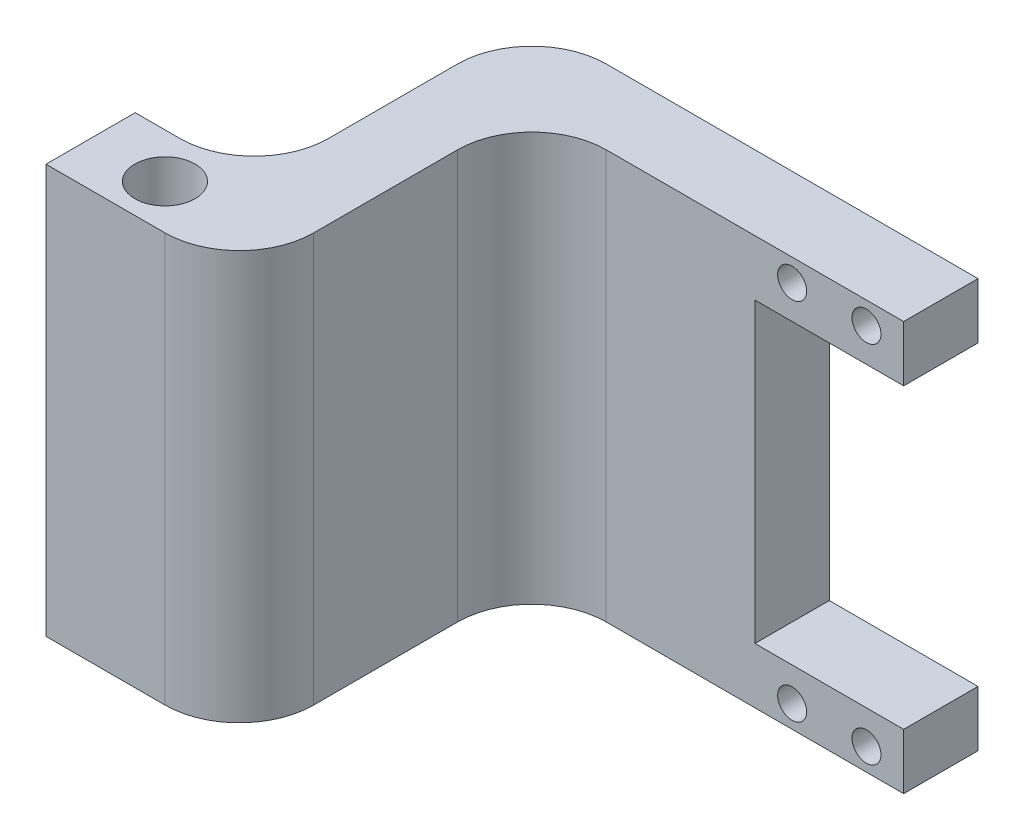
SolidWorks part; units mm, degrees
ref_plane "Ebene vorne" through (0, 0, 0) normal (0, 0, 1) x (1, 0, 0)
ref_plane "Ebene oben" through (0, 0, 0) normal (0, 1, 0) x (1, 0, 0)
ref_plane "Ebene rechts" through (0, 0, 0) normal (1, 0, 0) x (0, 0, -1)
sketch "Sketch1" plane through (0, 0, 0) normal (0, 0, 1) x (1, 0, 0)
  line L0 (-10, 24.5) -> (10, 24.5) construction
  line L5 (10, -20) -> (-10, -20)
  line L6 (10, -20) -> (10, 20) construction
  line L15 (10, 20) -> (-10, 20)
  line L16 (-10, -20) -> (-10, 20)
  line L17 (10, -20) -> (-10, 20) construction
  line L18 (10, 20) -> (-10, -20) construction
  line L19 (-10, 20) -> (10, 20)
  line L20 (-10, 20) -> (-10, 27.5)
  line L21 (-10, 27.5) -> (10, 27.5)
  line L22 (10, 20) -> (10, 27.5)
  line L23 (-10, 0) -> (10, 0) construction
  line L24 (-10, -24.5) -> (10, -24.5) construction
  line L25 (10, -20) -> (10, -27.5)
  line L26 (-10, -27.5) -> (10, -27.5)
  line L27 (-10, -20) -> (-10, -27.5)
  line L28 (-10, -20) -> (10, -20)
  line L29 (10, -20) -> (-10, -20)
  line L31 (-10, 27.5) -> (-40, 27.5)
  line L32 (-10, 27.5) -> (-10, -27.5)
  line L33 (-10, -27.5) -> (-40, -27.5)
  line L34 (-40, 27.5) -> (-40, -27.5)
  circle A0 centre (-5, 24.5) radius 1.95
  circle A1 centre (5, 24.5) radius 1.95
  circle A2 centre (5, -24.5) radius 1.95
  circle A3 centre (-5, -24.5) radius 1.95
  point P0 (0, 0)
  dimension "D5" = 3.9
  dimension "D1" = 20
  dimension "D2" = 40
  dimension "D3" = 7.5
  dimension "D4" = 4.5
  dimension "D6" = 10
  dimension "D7" = 5
  dimension "D8" = 30
extrude "Boss-Extrude2" add sketch "Sketch1" along normal blind 10 contours L31 L34 L33 L27 L16 L20 | L15 L22 L21 L20 A1 A0 | L5 L27 L26 L25 A2 A3
sketch "Sketch3" plane through (-40, 0, 0) normal (-1, 0, 0) x (0, 0, 1)
  line L1 (0, 27.5) -> (49.35, 27.5)
  line L2 (0, 27.5) -> (0, -27.5)
  line L3 (0, -27.5) -> (49.35, -27.5)
  line L4 (49.35, 27.5) -> (49.35, -27.5)
  dimension "D1" = 55
  dimension "D2" = 49.35
extrude "Boss-Extrude3" add sketch "Sketch3" along normal blind 10
sketch "Sketch4" plane through (0, -27.5, 0) normal (0, -1, 0) x (1, 0, 0)
  line L0 (-62, 49.35) -> (-50, 37.35) construction
  line L1 (-50, 49.35) -> (-62, 49.35)
  line L2 (-50, 49.35) -> (-50, 37.35)
  line L3 (-50, 37.35) -> (-62, 37.35)
  line L4 (-62, 49.35) -> (-62, 37.35)
  line L6 (-62, 49.35) -> (-66, 49.35)
  line L7 (-62, 49.35) -> (-62, 37.35)
  line L8 (-62, 37.35) -> (-66, 37.35)
  line L9 (-66, 49.35) -> (-66, 37.35)
  circle A0 centre (-56, 43.35) radius 4.05
  line M8 (-50, 49.35) -> (-50, 0)
  dimension "D3" = 8.1
  dimension "D1" = 12
  dimension "D2" = 12
  dimension "D4" = 4
extrude "Boss-Extrude4" add sketch "Sketch4" against normal up to surface (55 mm away) contours L0 L4 L3 A0 | L1 L0 A0 M8 | L6 L9 L8 L4
sketch "Sketch5" plane through (-66, 0, 0) normal (-1, 0, 0) x (0, 0, 1)
  line L0 (43.35, 27.5) -> (43.35, -27.5) construction
  line L1 (37.35, 27.5) -> (49.35, 27.5) construction
  line L2 (49.35, -27.5) -> (37.35, -27.5) construction
  circle A0 centre (43.35, 20) radius 1.45
  circle A1 centre (43.35, 0) radius 1.45
  circle A2 centre (43.35, -20) radius 1.45
  point P14 (43.35, 0)
  dimension "D1" = 2.9
  dimension "D2" = 20
  dimension "D3" = 20
extrude "Cut-Extrude1" cut sketch "Sketch5" against normal blind 10
fillet "Fillet1" radius 10 4 edges at (-50, 0, 37.35) (-40, 0, 10) (-40, 0, 49.35) (-50, 0, 0)
